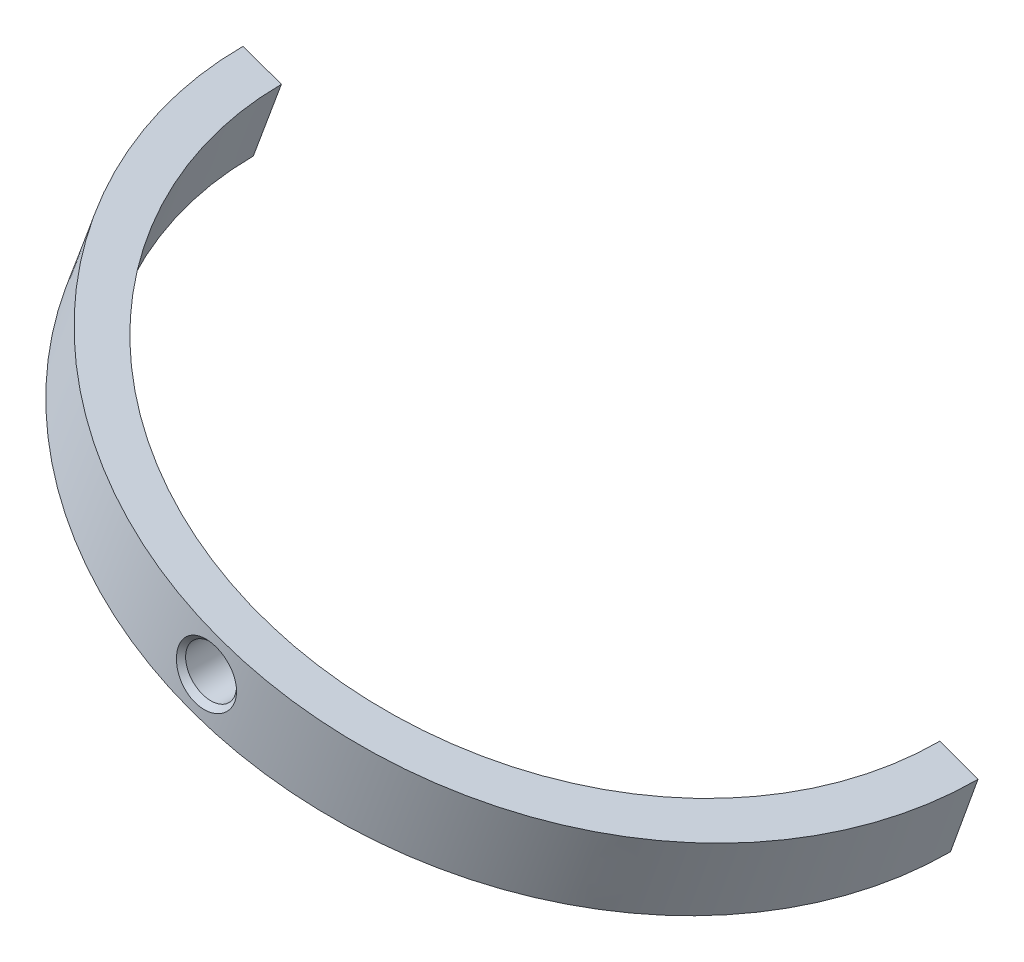
SolidWorks part; units mm, degrees
material "3.1645 (EN-AW 2030)"
ref_plane "Přední rovina" through (0, 0, 0) normal (0, 0, 1) x (1, 0, 0)
ref_plane "Horní rovina" through (0, 0, 0) normal (0, 1, 0) x (1, 0, 0)
ref_plane "Pravá rovina" through (0, 0, 0) normal (1, 0, 0) x (0, 0, -1)
sketch "Skica1" plane through (0, 0, 0) normal (0, 0, 1) x (1, 0, 0)
  line L0 (-393.3135, -15.83) -> (-357.1063, -29.0083) construction
  line L1 (-393.3135, -15.83) -> (-357.1063, -29.0083) construction
  line L2 (-361.5866, -31.6191) -> (-358.4905, -32.7612) construction
  line L4 (-358.4939, -32.7599) -> (-357.1406, -28.9958)
  line L8 (-357.1416, -28.9985) -> (-357.4799, -29.9396) construction
  line L9 (-359.02, -28.3118) -> (-357.1406, -28.9958)
  line L10 (-360.3703, -32.0678) -> (-359.02, -28.3118)
  line L11 (-358.4939, -32.7599) -> (-360.3703, -32.0678)
  line L12 (-372.8806, -16.0194) -> (-374.7984, -21.2885) construction
  line L13 (-372.8806, -16.0194) -> (-374.7984, -21.2885) construction
  dimension "D2" = 2
revolve "Rotovat1" add sketch "Skica1" angle 180 about L13
hole_wizard "M3 závit1" positions "3DSkica2" profile "Skica4" tap size "M3" standard "ISO" end condition up to next
sketch3d "3DSkica2"
  line L7 (-376.5783, -26.1777, 19.2447) -> (-376.5753, -26.1696, 17.2446) construction
  line L12 (-376.5783, -26.1777, 19.2447) -> (-362.5591, -31.2803, 19.245) construction
  line L15 (-360.3703, -32.0678, 0) -> (-358.4939, -32.7599, 0) construction
  line L16 (-376.5783, -26.1777, 19.2447) -> (-375.2102, -22.419, 19.2289) construction
  arc A4 (-394.6621, -19.5958, 0) -> (-358.4939, -32.7599, 0) centre (-376.578, -26.1779, 0) ccw construction
  arc A5 (-392.7797, -20.2717, 0) -> (-360.3703, -32.0678, 0) centre (-376.575, -26.1698, 0) ccw construction
  arc A9 (-393.2792, -15.8425, 0) -> (-357.1406, -28.9958, 0) centre (-375.2099, -22.4191, 0) ccw construction
  point P36 (-369.9959, -8.0938, 0)
  point P40 (-370.677, -9.9651, 0)
  point P76 (-368.6332, -4.3499, 0)
  point P77 (-375.8943, -24.2984, 19.2368)
  point P80 (-375.8943, -24.2984, 19.2368)
  point P82 (-375.8943, -24.2984, 19.2368)
sketch "Skica4" plane through (-375.8943, -24.2984, 19.2368) normal (0.7071, 0.7071, -0.0036) x (0.7071, -0.7071, 0.0017)
  line L0 (0, 0) -> (0, 19.289)
  line L1 (0, 19.289) -> (1.25, 19.289)
  line L2 (1.25, 19.289) -> (1.25, 0.275)
  line L3 (1.25, 0.275) -> (1.525, 0)
  line L5 (1.525, 0) -> (0, 0)
  line L6 (-1.25, 0.275) -> (-1.525, 0) construction
  line L11 (0, -6.35) -> (0, 107.95) construction
  dimension "Průměr závitníku" = 2.5
  dimension "Hloubka závitníku" = 19.289
  dimension "Průměr blíz. kuž. zahloubení" = 3.05
  dimension "Úhel blíz. kuž. zahloubení" = 90
cosmetic thread "Závit díry5"
